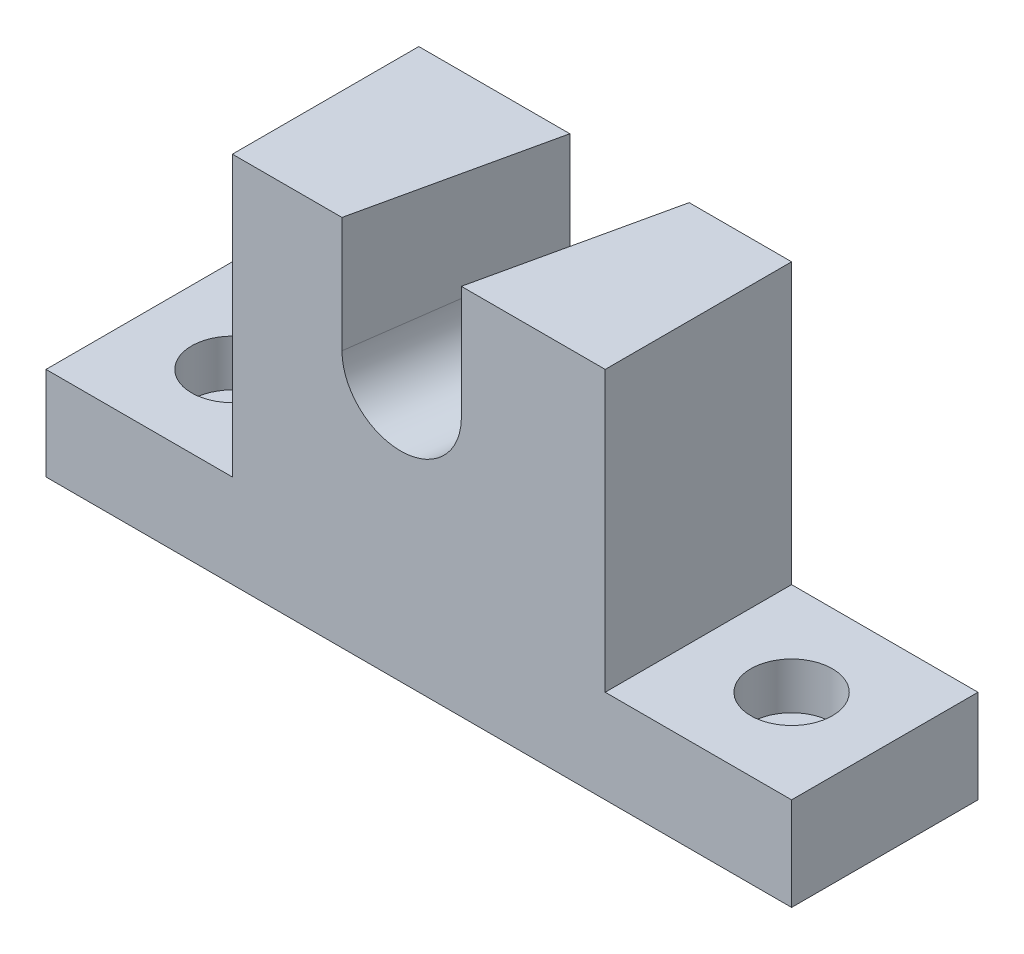
SolidWorks part; units mm, degrees
ref_plane "Front Plane" through (0, 0, 0) normal (0, 0, 1) x (1, 0, 0)
ref_plane "Top Plane" through (0, 0, 0) normal (0, 1, 0) x (1, 0, 0)
ref_plane "Right Plane" through (0, 0, 0) normal (1, 0, 0) x (0, 0, -1)
sketch "Sketch1" plane through (0, 0, 0) normal (0, 0, 1) x (1, 0, 0)
  line L0 (25.4, 12.7) -> (50.8, 12.7)
  line L1 (-50.8, 12.7) -> (-25.4, 12.7)
  line L2 (-50.8, 12.7) -> (-50.8, 0)
  line L3 (-50.8, 0) -> (50.8, 0)
  line L4 (50.8, 12.7) -> (50.8, 0)
  line L5 (-25.4, 50.8) -> (25.4, 50.8)
  line L6 (-25.4, 50.8) -> (-25.4, 12.7)
  line L8 (25.4, 50.8) -> (25.4, 12.7)
  line L9 (0, 0) -> (0, 42.1156) construction
  point P8 (0, 0)
  dimension "D1" = 101.6
  dimension "D2" = 50.8
  dimension "D3" = 12.7
  dimension "D4" = 50.8
extrude "Boss-Extrude1" add sketch "Sketch1" along normal blind 25.4
sketch "Sketch2" plane through (0, 0, 0) normal (0, 1, 0) x (1, 0, 0)
  line L0 (-38.1, 0) -> (-38.1, -25.4) construction
  line L1 (-25.4, 0) -> (-50.8, 0) construction
  line L2 (-25.4, -25.4) -> (-50.8, -25.4) construction
  line L4 (50.8, 0) -> (25.4, 0) construction
  line L5 (38.1, 0) -> (38.1, -25.4) construction
  line L6 (50.8, -25.4) -> (25.4, -25.4) construction
  point P12 (-38.1, -12.7)
  point P13 (38.1, -12.7)
hole_wizard "CBORE for 1/4 Socket Head Cap Screw1" positions "Sketch3" profile "Sketch4" counterbore size "1/4" standard "ANSI Inch" end condition through all
sketch "Sketch3" plane through (0, 12.7, 0) normal (0, 1, 0) x (1, 0, 0)
  point P0 (-38.1, -12.7)
  point P3 (38.1, -12.7)
sketch "Sketch4" plane through (-38.1, 12.7, 12.7) normal (1, 0, 0) x (0, 0, 1)
  line L0 (0, 0) -> (0, 12.7)
  line L1 (0, 12.7) -> (3.3782, 12.7)
  line L3 (3.3782, 12.7) -> (3.3782, 6.35)
  line L4 (3.3782, 6.35) -> (5.5562, 6.35)
  line L5 (5.5562, 6.35) -> (5.5562, 0)
  line L7 (5.5562, 0) -> (0, 0)
  line L11 (0, -6.35) -> (0, 107.95) construction
  dimension "Thru Hole Dia." = 6.7564
  dimension "Thru Hole Depth" = 12.7
  dimension "C'Bore Dia." = 11.1125
  dimension "C'Bore Depth" = 6.35
sketch3d "3DSketch1"
  line L0 (-10.4425, 32.4644, 61.8504) -> (10.4804, 39.5001, -32.2338)
  point P2 (-43.433, 25.9478, 64.5959)
  point P3 (26.6039, 39.1119, -32.1396)
  point P4 (-10.7505, 25.5084, 64.5959)
  point P5 (7.5986, 42.1329, -32.1396)
  point P6 (10.6692, 29.8764, 54.8491)
  point P7 (-4.8854, 30.3551, 60.5472)
  point P8 (-2.5031, 44.1075, -29.0679)
  point P9 (10.4804, 39.5001, -32.2338)
  point P10 (-10.4425, 32.4644, 61.8504)
ref_plane "Plane1" through (-10.4425, 32.4644, 61.8504) normal (0.2165, 0.0728, -0.9736) x (-0.9762, 0.0266, -0.2151)
sketch "Sketch6" plane through (-10.4425, 32.4644, 61.8504) normal (0.2165, 0.0728, -0.9736) x (-0.9762, 0.0266, -0.2151)
  line L0 (-7.9347, 0.2117) -> (-6.7951, 42.9154)
  line L1 (-22.2117, -24.0901) -> (-21.198, 13.8953) construction
  line L2 (7.9347, -0.2117) -> (9.0742, 42.4919)
  line L3 (28.3943, 13.3751) -> (27.3807, -24.6103) construction
  line L4 (-6.7951, 42.9154) -> (9.0742, 42.4919)
  circle A0 centre (0, 0) radius 7.9375
  point P11 (0, 0)
  point P12 (0, 0)
  dimension "D1" = 15.875
extrude "Cut-Extrude2" cut sketch "Sketch6" along normal through all contours A0 | A0 L2 L4 L0
